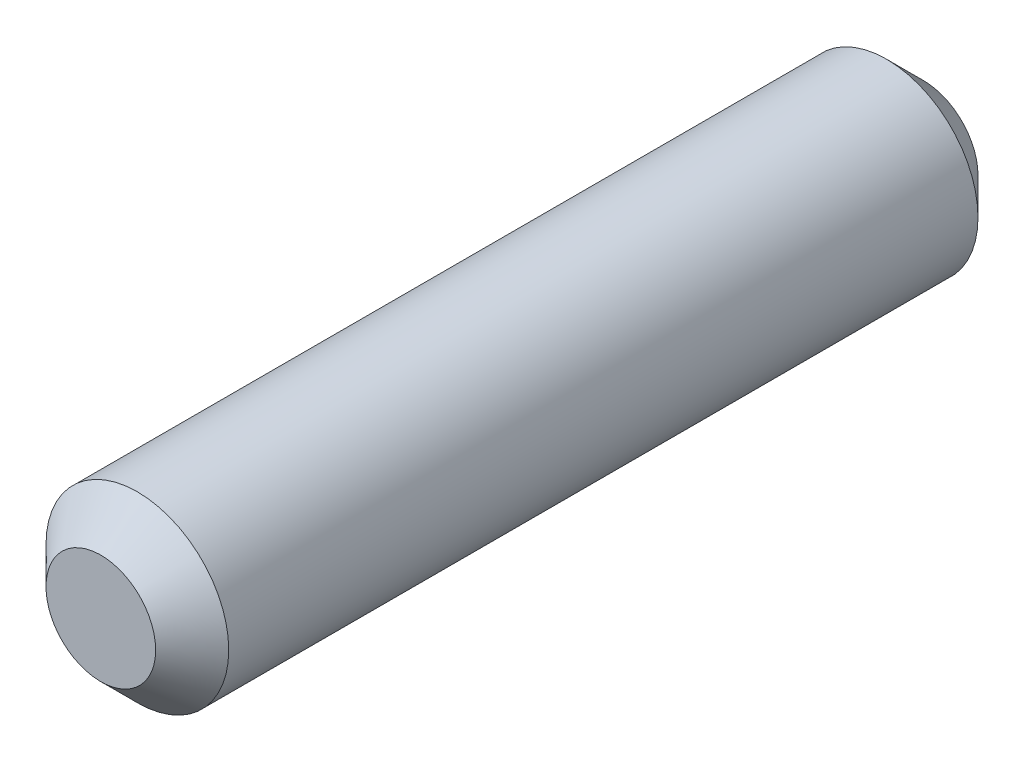
SolidWorks part; units mm, degrees
material "AISI 1020 Steel, Cold Rolled"
ref_plane "Front Plane" through (0, 0, 0) normal (0, 0, 1) x (1, 0, 0)
ref_plane "Top Plane" through (0, 0, 0) normal (0, 1, 0) x (1, 0, 0)
ref_plane "Right Plane" through (0, 0, 0) normal (1, 0, 0) x (0, 0, -1)
sketch "Sketch1" plane through (0, 0, 0) normal (0, 0, 1) x (1, 0, 0)
  circle A0 centre (0, 0) radius 5
  dimension "D1" = 10
extrude "Boss-Extrude1" add sketch "Sketch1" along normal blind 45
chamfer "Chamfer1" distance 2 angle 45 2 edges at (5, 0, 0) (5, 0, 45)
